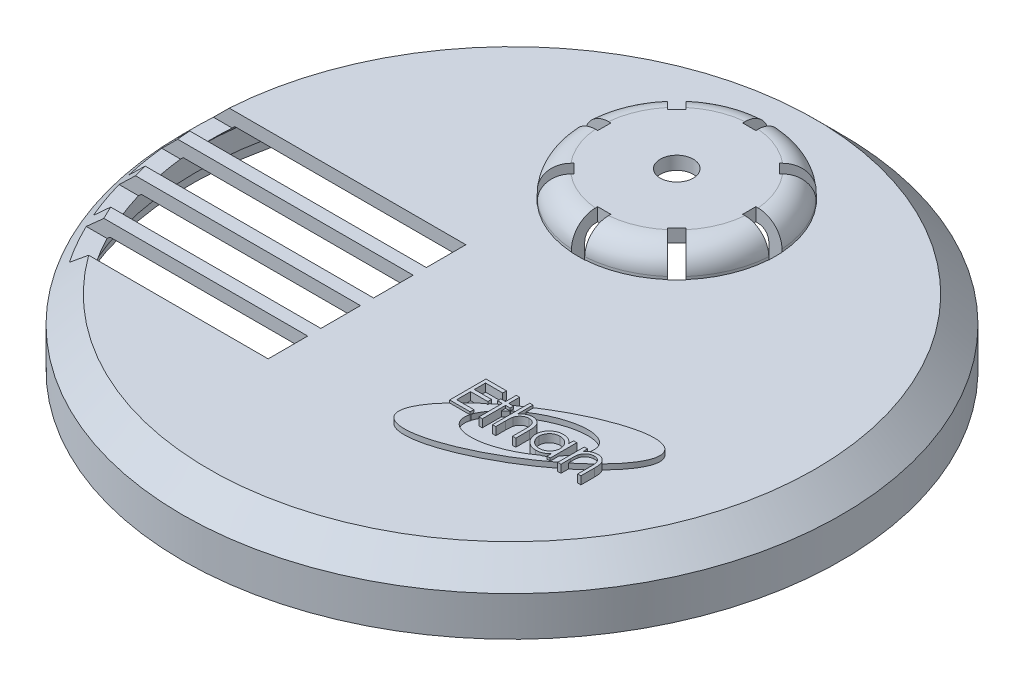
SolidWorks part; units mm, degrees
ref_plane "Front Plane" through (0, 0, 0) normal (0, 0, 1) x (1, 0, 0)
ref_plane "Top Plane" through (0, 0, 0) normal (0, 1, 0) x (1, 0, 0)
ref_plane "Right Plane" through (0, 0, 0) normal (1, 0, 0) x (0, 0, -1)
sketch "Sketch2" plane through (0, 0, 0) normal (0, 1, 0) x (1, 0, 0)
  circle A0 centre (0, 0) radius 31.75
  dimension "D1" = 63.5
extrude "Boss-Extrude1" add sketch "Sketch2" along normal blind 6.35 contours A0
chamfer "Chamfer1" distance 2.54 angle 45 1 edges at (0, 6.35, 31.75)
sketch "Sketch3" plane through (0, 6.35, 0) normal (0, 1, 0) x (1, 0, 0)
  circle A0 centre (0, 15.875) radius 9.525
  point P2 (0, 0)
  dimension "D1" = 19.05
  dimension "D2" = 15.875
extrude "Boss-Extrude2" add sketch "Sketch3" along normal blind 2.54
fillet "Fillet1" radius 2.286 1 edges at (0, 8.89, -6.35)
shell "Shell1" thickness 1.27
sketch "Sketch4" plane through (0, 0, 0) normal (0, -1, 0) x (1, 0, 0)
  circle A4 centre (0, 0) radius 30.988
  circle A5 centre (0, 0) radius 30.988
  dimension "D1" = 0.762
extrude "Cut-Extrude1" cut sketch "Sketch4" against normal blind 1.27
sketch "Sketch5" plane through (0, 8.89, 0) normal (0, 1, 0) x (1, 0, 0)
  circle A0 centre (0, 15.875) radius 1.5875
  dimension "D1" = 3.175
extrude "Cut-Extrude2" cut sketch "Sketch5" against normal through all
sketch "Sketch6" plane through (0, 8.89, 0) normal (0, 1, 0) x (1, 0, 0)
  line L0 (0, 15.875) -> (8.255, 15.875) construction
  line L2 (6.985, 15.24) -> (9.525, 15.24)
  line L3 (6.985, 15.24) -> (6.985, 16.51)
  line L4 (6.985, 16.51) -> (9.525, 16.51)
  line L5 (9.525, 15.24) -> (9.525, 16.51)
  line L6 (6.985, 15.24) -> (9.525, 16.51) construction
  line L7 (6.985, 16.51) -> (9.525, 15.24) construction
  circle A0 centre (0, 15.875) radius 9.525 construction
  dimension "D1" = 2.54
  dimension "D2" = 1.27
extrude "Cut-Extrude3" cut sketch "Sketch6" against normal through all
pattern_circular "CirPattern1" count 8 over 360 about axis through (0, 0, -15.875) along (0, 1, 0) of "Cut-Extrude3"
sketch "Sketch7" plane through (0, 6.35, 0) normal (0, 1, 0) x (1, 0, 0)
  line L0 (-19.05, 0) -> (0, 0) construction
  line L1 (-31.75, -1.905) -> (-6.35, -1.905)
  line L2 (-31.75, -1.905) -> (-31.75, 1.905)
  line L3 (-31.75, 1.905) -> (-6.35, 1.905)
  line L4 (-6.35, -1.905) -> (-6.35, 1.905)
  line L5 (-31.75, -1.905) -> (-6.35, 1.905) construction
  line L6 (-31.75, 1.905) -> (-6.35, -1.905) construction
  point P0 (-19.05, 0)
  dimension "D1" = 6.35
  dimension "D2" = 3.81
  dimension "D3" = 25.4
extrude "Cut-Extrude4" cut sketch "Sketch7" against normal blind 1.524
pattern_linear "LPattern1" count 4 spacing 5.08 along (0, 0, 1) of "Cut-Extrude4"
sketch "Sketch8" plane through (0, 6.35, 0) normal (0, 1, 0) x (1, 0, 0)
  line L0 (6.1356, -12.5911) -> (21.3729, -12.5911) construction
  text T0 "Ethan" font "Century Gothic" height 3.5
extrude "Boss-Extrude3" add sketch "Sketch8" along normal blind 0.762
sketch "Sketch9" plane through (0, 6.35, 0) normal (0, 1, 0) x (1, 0, 0)
  line L0 (12.9561, -11.2849) -> (12.9561, -12.5911) construction
  line L1 (12.9561, -11.2849) -> (12.9561, -12.5911) construction
  ellipse E0 centre (12.9561, -11.2849) end of major axis (20.9483, -6.2533) minor radius 3.0153
  ellipse E1 centre (12.9561, -11.2849) end of major axis (17.2984, -8.9334) minor radius 2.3556
extrude "Boss-Extrude4" add sketch "Sketch9" along normal blind 0.508
